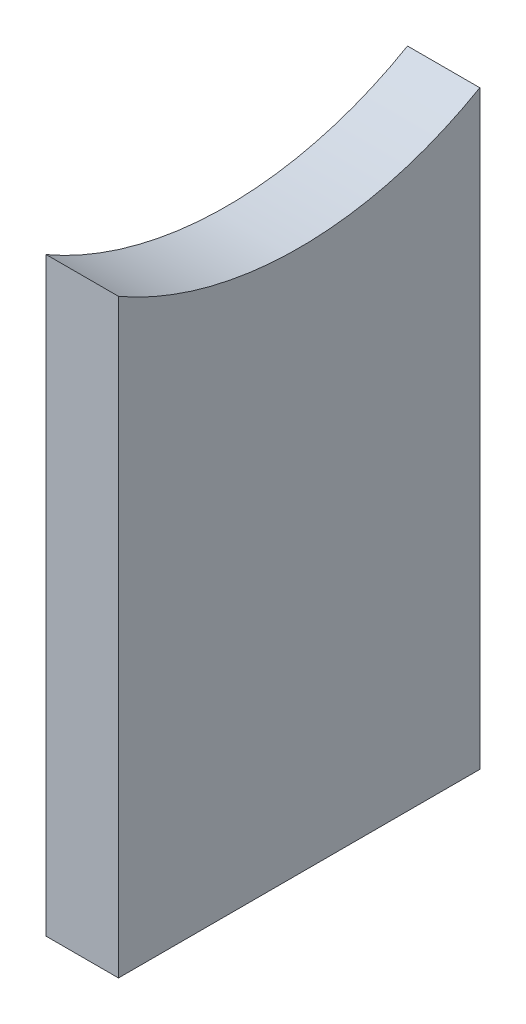
SolidWorks part; units mm, degrees
ref_plane "Front Plane" through (0, 0, 0) normal (0, 0, 1) x (1, 0, 0)
ref_plane "Top Plane" through (0, 0, 0) normal (0, 1, 0) x (1, 0, 0)
ref_plane "Right Plane" through (0, 0, 0) normal (1, 0, 0) x (0, 0, -1)
sketch "Sketch1" plane through (0, 0, 0) normal (1, 0, 0) x (0, 0, -1)
  line L1 (0, 0) -> (25.4, 0)
  line L2 (0, 0) -> (0, 41.503)
  line L4 (25.4, 0) -> (25.4, 41.503)
  arc A0 (0, 41.503) -> (25.4, 41.503) centre (12.7, 63.5) ccw
  point P6 (12.7, 38.1)
  point P7 (12.7, 0)
  dimension "D3" = 25.4
  dimension "D2" = 25.4
  dimension "D1" = 38.1
extrude "Boss-Extrude1" add sketch "Sketch1" along normal blind 5.08
equation "\"Foamcore\"= 0.2in"
equation "\"MDF\"= 0.2in"
equation "\"D1@Boss-Extrude1\"=\"Foamcore\""
equation "\"D3@Sketch1\"=\"TubeR\"+\"Foamcore\""
equation "\"TubeR\"= 0.8in"
